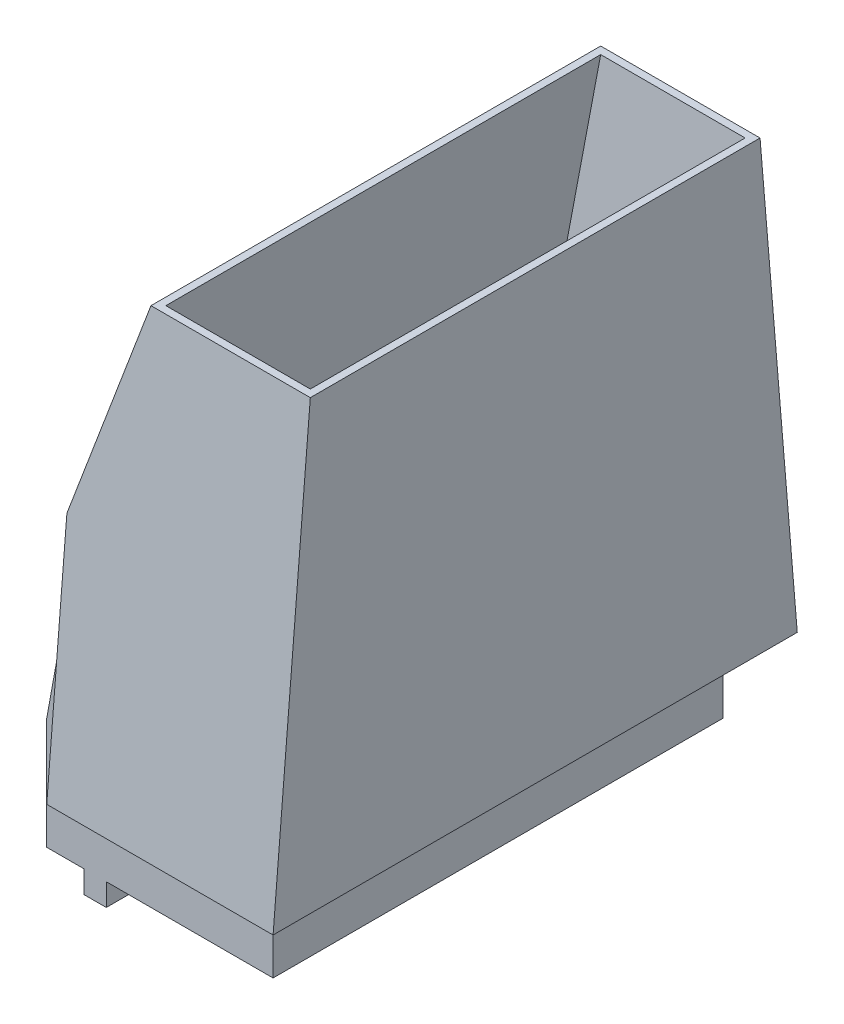
SolidWorks part; units mm, degrees
ref_plane "Ebene vorne" through (0, 0, 0) normal (0, 0, 1) x (1, 0, 0)
ref_plane "Ebene oben" through (0, 0, 0) normal (0, 1, 0) x (1, 0, 0)
ref_plane "Ebene rechts" through (0, 0, 0) normal (1, 0, 0) x (0, 0, -1)
sketch "Skizze1" plane through (0, 0, 0) normal (0, 0, 1) x (1, 0, 0)
  line L0 (14, 14.875) -> (14, 29.875)
  line L1 (24, 84.875) -> (23, 84.875)
  line L2 (24, 84.875) -> (24, 24.875)
  line L3 (19, 24.875) -> (24, 24.875)
  line L4 (19, 24.875) -> (19, 14.875)
  line L5 (19, 14.875) -> (14, 14.875)
  line L6 (23, 84.875) -> (14, 29.875)
  dimension "D1" = 10
  dimension "D2" = 5
  dimension "D3" = 15
  dimension "D4" = 5
  dimension "D5" = 60
  dimension "D6" = 1
extrude "Aufsatz-Linear austragen1" add sketch "Skizze1" along normal blind 60.4
sketch "Skizze2" plane through (24, 0, 0) normal (1, 0, 0) x (0, 0, -1)
  line L0 (-59.4, 84.875) -> (-60.4, 84.875)
  line L1 (-60.4, 84.875) -> (-65.4, 24.875)
  line L2 (0, 24.875) -> (0, 14.875)
  line L3 (-60.4, 14.875) -> (-60.4, 24.875) construction
  line L4 (-55.2, 29.875) -> (-55.2, 14.875)
  line L5 (-55.2, 14.875) -> (-60.4, 14.875)
  line L6 (-60.4, 14.875) -> (-60.4, 24.875)
  line L7 (-60.4, 24.875) -> (0, 24.875) construction
  line L8 (-60.4, 24.875) -> (-65.4, 24.875)
  line L9 (0, 14.875) -> (-5.2, 14.875)
  line L10 (-5.2, 14.875) -> (-5.2, 29.875)
  line L11 (-60.4, 84.875) -> (0, 84.875) construction
  line L12 (-1, 84.875) -> (0, 84.875)
  line L13 (5, 24.875) -> (0, 24.875)
  line L14 (-59.4, 84.875) -> (-55.2, 29.875)
  line L15 (0, 84.875) -> (5, 24.875)
  line L16 (-1, 84.875) -> (-5.2, 29.875)
  point P2 (-60.4, 19.875)
  dimension "D1" = 5.2
  dimension "D2" = 0
  dimension "D3" = 5
  dimension "D4" = 10
  dimension "D5" = 15
  dimension "D6" = 5.2
  dimension "D7" = 15
  dimension "D8" = 10
  dimension "D9" = 5
extrude "Aufsatz-Linear austragen2" add sketch "Skizze2" against normal blind 30.4
sketch "Skizze3" plane through (0, 0, 5.2) normal (0, 0, 1) x (1, 0, 0)
  line L0 (-3.4, 29.875) -> (-3.4, 14.875)
  line L1 (-11.4, 29.875) -> (-1.4, 84.875)
  line L2 (-6.4, 14.875) -> (14, 14.875) construction
  line L3 (-3.4, 29.875) -> (3.6, 84.875)
  line L5 (-1.4, 84.875) -> (3.6, 84.875)
  line L6 (-11.4, 14.875) -> (-11.4, 29.875)
  line L9 (-3.4, 14.875) -> (-3.4, 11.875)
  line L10 (-3.4, 11.875) -> (-6.4, 11.875)
  line L11 (-6.4, 11.875) -> (-6.4, 14.875)
  line L12 (-6.4, 14.875) -> (-11.4, 14.875)
  dimension "D1" = 3
  dimension "D2" = 3
  dimension "D3" = 15
  dimension "D4" = 5
  dimension "D5" = 15
  dimension "D6" = 70
  dimension "D7" = 5
  dimension "D8" = 5
extrude "Aufsatz-Linear austragen3" add sketch "Skizze3" along normal blind 55.2 and the other way blind 5.2
sketch "Skizze4" plane through (0, 0, 60.4) normal (0, 0, 1) x (1, 0, 0)
  line L0 (24, 14.875) -> (24, 24.875)
  line L1 (24, 14.875) -> (19, 14.875)
  line L2 (-3.4, 14.875) -> (24, 14.875) construction
  line L3 (19, 14.875) -> (19, 24.875)
  line L4 (24, 24.875) -> (-6.4, 24.875) construction
  line L5 (19, 24.875) -> (24, 24.875)
  dimension "D1" = 5
extrude "Schnitt-Linear austragen1" cut sketch "Skizze4" against normal through all
sketch "Skizze7" plane through (0, 0, 0) normal (0, 0, -1) x (-1, 0, 0)
  line L1 (6.4, 57.375) -> (-2.6, 84.875)
  line L2 (-24, 84.875) -> (6.4, 84.875) construction
  line L5 (-2.6, 84.875) -> (6.4, 84.875)
  line L6 (6.4, 84.875) -> (6.4, 57.375)
  dimension "D1" = 9
extrude "Schnitt-Linear austragen4" cut sketch "Skizze7" against normal through all and the other way through all
